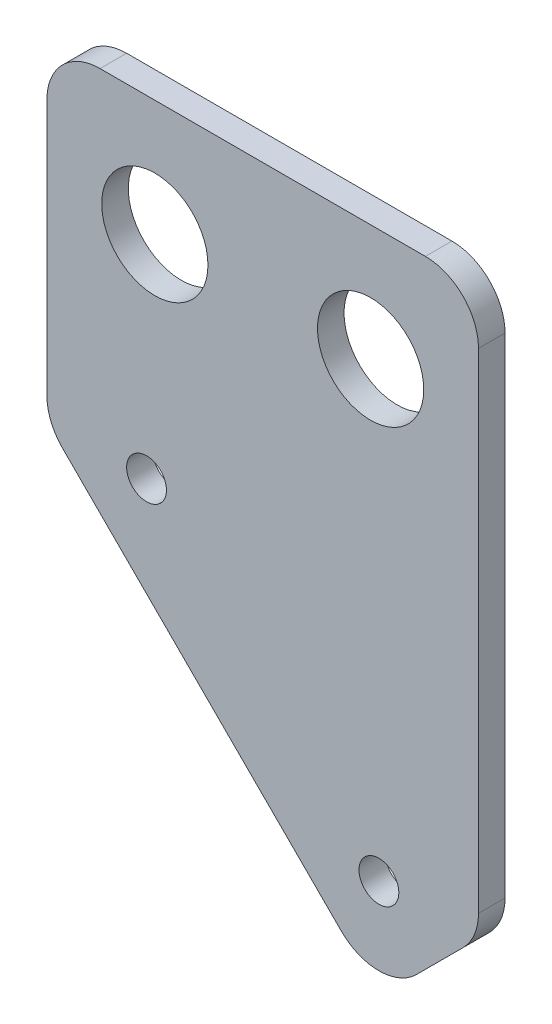
SolidWorks part; units mm, degrees
ref_plane "Alzado" through (0, 0, 0) normal (0, 0, 1) x (1, 0, 0)
ref_plane "Planta" through (0, 0, 0) normal (0, 1, 0) x (1, 0, 0)
ref_plane "Vista lateral" through (0, 0, 0) normal (1, 0, 0) x (0, 0, -1)
sketch "Croquis1" plane through (0, 0, 0) normal (0, 0, 1) x (1, 0, 0)
  line L0 (0, 0) -> (17.5, 0) construction
  line L1 (17.5, 0) -> (17.5, -17.5) construction
  line L2 (17.5, -17.5) -> (25, -17.5) construction
  line L3 (25, -17.5) -> (17.5, -17.5) construction
  line L4 (17.5, -17.5) -> (17.5, -25) construction
  line L5 (0, 0) -> (0, 7.5) construction
  line L6 (0, 0) -> (-7.5, 0) construction
  line L7 (0, 7.5) -> (25, 7.5) construction
  line L8 (25, 7.5) -> (25, -17.5) construction
  line L9 (17.5, -25) -> (25, -17.5) construction
  line L10 (23.8284, -18.6716) -> (20.3284, -22.1716)
  line L11 (14.6716, -22.1716) -> (-6.3284, -1.1716)
  line L12 (-7.5, 1.6569) -> (-7.5, 21)
  line L13 (-3.5, 25) -> (21, 25)
  line L14 (25, 21) -> (25, -15.8431)
  line L15 (-7.5, 25) -> (25, 7.5) construction
  line L16 (25, 7.5) -> (8.75, 16.25) construction
  line L17 (8.75, 16.25) -> (8.75, 25) construction
  line L18 (8.75, 25) -> (25, 7.5) construction
  line L19 (25, 7.5) -> (25, 25) construction
  line L20 (25, 25) -> (8.75, 7.5) construction
  line L21 (8.75, 7.5) -> (-7.5, 25) construction
  line L22 (8.75, 25) -> (-7.5, 7.5) construction
  circle A11 centre (0, 0) radius 1.5
  circle A12 centre (17.5, -17.5) radius 1.5
  circle A13 centre (0.625, 16.25) radius 4
  circle A14 centre (16.875, 16.25) radius 4
  arc A15 (-7.5, 1.6569) -> (-6.3284, -1.1716) centre (-3.5, 1.6569) ccw
  arc A16 (23.8284, -18.6716) -> (25, -15.8431) centre (21, -15.8431) ccw
  arc A17 (20.3284, -22.1716) -> (14.6716, -22.1716) centre (17.5, -19.3431) cw
  arc A18 (21, 25) -> (25, 21) centre (21, 21) cw
  arc A19 (-7.5, 21) -> (-3.5, 25) centre (-3.5, 21) cw
  dimension "D1" = 4
extrude "Saliente-Extruir1" add sketch "Croquis1" along normal blind 2
